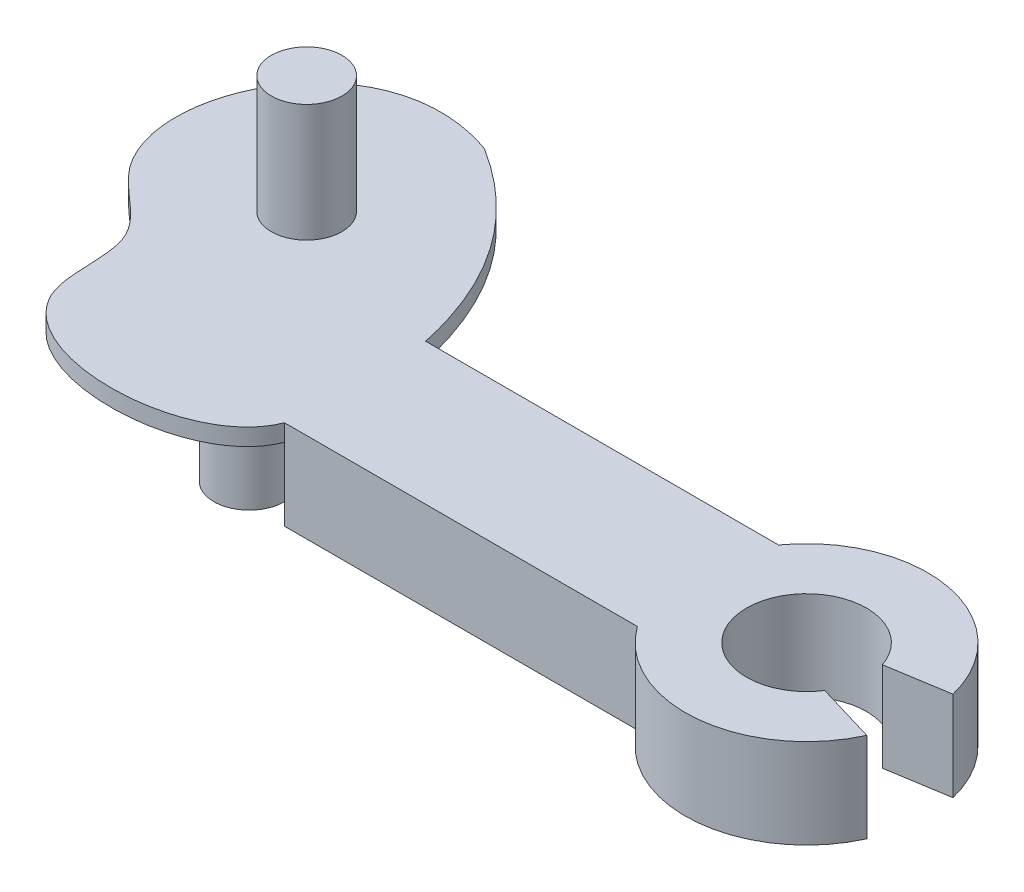
SolidWorks part; units mm, degrees
ref_plane "Front Plane" through (0, 0, 0) normal (0, 0, 1) x (1, 0, 0)
ref_plane "Top Plane" through (0, 0, 0) normal (0, 1, 0) x (1, 0, 0)
ref_plane "Right Plane" through (0, 0, 0) normal (1, 0, 0) x (0, 0, -1)
sketch "Sketch1" plane through (0, 0, 0) normal (0, 1, 0) x (1, 0, 0)
  line L0 (0, 0) -> (10, 0) construction
  line L1 (10, 0) -> (12.794, 0)
  line L2 (0, 0) -> (10, 0) construction
  line L3 (10, -2) -> (10, 2)
  line L4 (16.1332, 0.8101) -> (14.4086, 0.5319)
  line L5 (10, -2) -> (0, -2)
  line L6 (10, -2) -> (10, 2)
  line L7 (10, 2) -> (0, 2)
  line L8 (0, -2) -> (0, 2)
  line L9 (-6.5043, -2) -> (-0.5043, 2.6) construction
  line L10 (0, -2) -> (-6.5043, -2) construction
  line L11 (15.9224, -1.4212) -> (14.2261, -0.916)
  circle A0 centre (-3.5043, 0.3) radius 1 construction
  circle A1 centre (12.794, 0) radius 3.406 construction
  arc A2 (10, 2) -> (16.1332, 0.8101) centre (12.794, 0) cw
  arc A3 (10, -2) -> (15.9224, -1.4212) centre (12.794, 0) ccw
  circle A4 centre (12.794, 0) radius 1.7 construction
  arc A5 (14.2261, -0.916) -> (14.4169, 0.506) centre (12.794, 0) cw
  spline S0 degree 3 poles (0, -2) (-0.807, -4.0986) (-7.3608, -4.1963) (-6.3435, 0.5483) (-10.7782, 2.929) (-8.0517, 9.0455) (-3.8921, 7.5585) knots 0 0 0 0 0.35586 0.470048 0.583543 1 1 1 1
  spline S1 degree 2 poles (-3.8921, 7.5585) (-0.7715, 5.6017) (0, 2) knots 0 0 0 1 1 1
  point P6 (10, 0)
  dimension "D7" = 2
  dimension "D3" = 6.812
  dimension "D5" = 3.4
  dimension "D1" = 10
  dimension "D2" = 2.794
  dimension "D4" = 4
  dimension "D6" = 6
  dimension "D8" = 1.7468
extrude "Boss-Extrude2" add sketch "Sketch1" along normal blind 2.54 contours S1 S0 L8 | L8 L5 L3 L7 | L11 A5 L1 L3 A3 | L1 A5 L4 A2 L3
ref_plane "Plane1" through (0, 2.54, 0) normal (0, 1, 0) x (1, 0, 0)
sketch "Sketch3" plane through (0, 2.54, 0) normal (0, 1, 0) x (1, 0, 0)
  line L0 (0, 0) -> (-3, 0)
  circle A0 centre (-3, 0) radius 1
  dimension "D2" = 2
  dimension "D1" = 3
extrude "Boss-Extrude3" add sketch "Sketch3" along normal blind 1.5
ref_plane "Plane2" through (0, 0, 0) normal (0, -1, 0) x (-1, 0, 0)
sketch "Sketch4" plane through (0, 0, 0) normal (0, -1, 0) x (-1, 0, 0)
  line L0 (0, 0) -> (4.8724, 3.5013) construction
  line L2 (0, 0) -> (4.8724, 0) construction
  circle A0 centre (4.8724, 3.5013) radius 1
  dimension "D4" = 2
  dimension "D1" = 6
  dimension "D2" = 3.5013
  dimension "D3" = 35.701
extrude "Boss-Extrude5" add sketch "Sketch4" along normal blind 1.5 contours A0
ref_plane "Plane3" through (0, 2.02, 0) normal (0, 1, 0) x (1, 0, 0)
sketch "Sketch6" plane through (0, 2.02, 0) normal (0, 1, 0) x (1, 0, 0)
  line L0 (-3, 1) -> (-3, -1) construction
  line L1 (-4, 0) -> (-2, 0) construction
  line L2 (0, 8.8591) -> (0, 2)
  line L3 (-11.0926, 8.8591) -> (0, 8.8591)
  line L4 (-11.0926, 8.8591) -> (-11.0926, -4.6725)
  line L5 (-11.0926, -4.6725) -> (0, -4.6725)
  line L7 (0, -2) -> (0, -4.6725)
  circle A0 centre (-3, 0) radius 1 construction
  circle A1 centre (-3, 0) radius 1 construction
  circle A2 centre (-3, 0) radius 1
  spline S0 degree 2 poles (0, 2) (2.1752, 0.2382) (0, -2) knots 0 0 0 1 1 1
ref_plane "Plane4" through (0, 2.54, 0) normal (0, 1, 0) x (1, 0, 0)
sketch "Sketch7" plane through (0, 2.54, 0) normal (0, 1, 0) x (1, 0, 0)
  line L0 (-4.8724, 2.5013) -> (-4.8724, 4.5013) construction
  line L1 (-5.8724, 3.5013) -> (-3.8724, 3.5013) construction
  circle A0 centre (-4.8724, 3.5013) radius 1 construction
  circle A1 centre (-4.8724, 3.5013) radius 1 construction
  circle A2 centre (-4.8724, 3.5013) radius 1
extrude "Boss-Extrude6" add sketch "Sketch7" along normal blind 3.33
ref_plane "Plane5" through (0, 0, 0) normal (0, -1, 0) x (-1, 0, 0)
sketch "Sketch8" plane through (0, 0, 0) normal (0, -1, 0) x (-1, 0, 0)
  circle A0 centre (3, 0) radius 1
extrude "Boss-Extrude7" add sketch "Sketch8" along normal blind 1.3996
sketch "Sketch9" plane through (0, 0, 0) normal (0, -1, 0) x (-1, 0, 0)
  line L0 (0, 8.8591) -> (0, 2)
  line L1 (0, -4.6725) -> (11.0926, -4.6725)
  line L3 (0, 8.8591) -> (11.0926, 8.8591)
  line L4 (11.0926, -4.6725) -> (11.0926, 8.8591)
  line L5 (0, -2) -> (0, -4.6725)
  circle A0 centre (3, 0) radius 1
  spline S0 degree 2 poles (0, 2) (-2.1752, 0.2382) (0, -2) knots 0 0 0 1 1 1
extrude "Cut-Extrude1" cut sketch "Sketch9" against normal blind 2.06 and the other way blind 3.33
ref_plane "Plane6" through (0, 2.54, 0) normal (0, 1, 0) x (1, 0, 0)
sketch "Sketch10" plane through (0, 2.54, 0) normal (0, 1, 0) x (1, 0, 0)
  circle A0 centre (-2.9409, -0.1663) radius 1.8621
extrude "Cut-Extrude2" cut sketch "Sketch10" along normal blind 2.06
